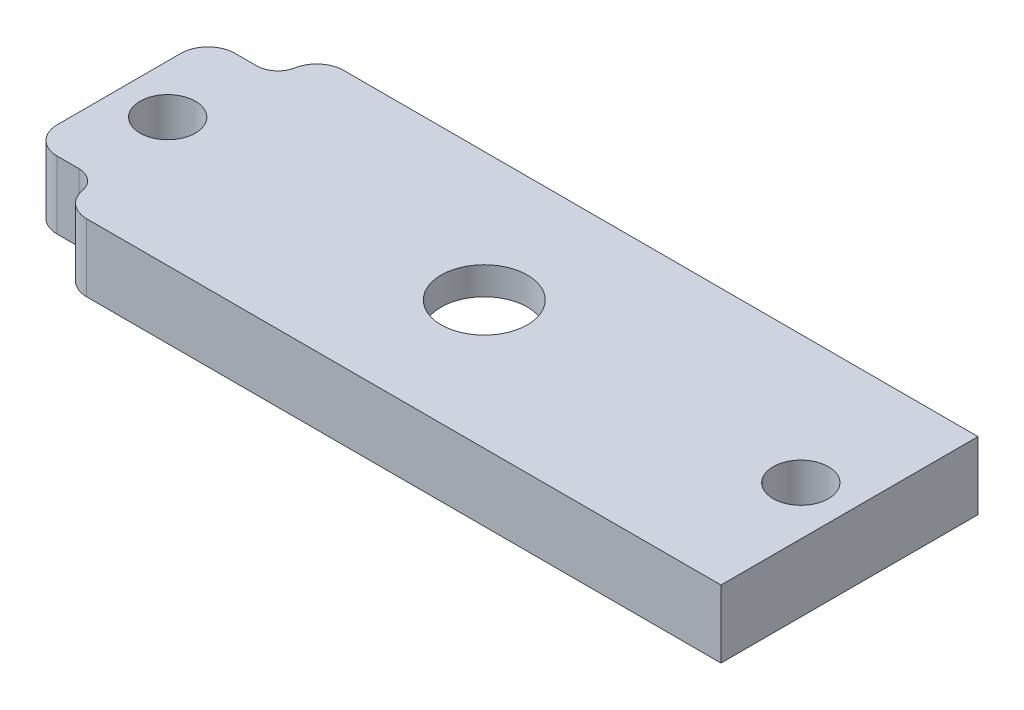
SolidWorks part; units mm, degrees
ref_plane "Front Plane" through (0, 0, 0) normal (0, 0, 1) x (1, 0, 0)
ref_plane "Top Plane" through (0, 0, 0) normal (0, 1, 0) x (1, 0, 0)
ref_plane "Right Plane" through (0, 0, 0) normal (1, 0, 0) x (0, 0, -1)
sketch "Sketch2" plane through (0, 0, 0) normal (0, 1, 0) x (1, 0, 0)
  line L1 (0, 0) -> (68.58, 0)
  line L2 (0, 0) -> (0, 24.13)
  line L3 (0, 24.13) -> (68.58, 24.13)
  line L4 (68.58, 0) -> (68.58, 24.13)
  circle A0 centre (4.57, 12.065) radius 2.6
  circle A1 centre (64.01, 12.065) radius 2.6
  point P10 (68.58, 12.065)
  dimension "D4" = 5.2
  dimension "D1" = 68.58
  dimension "D2" = 24.13
  dimension "D3" = 4.57
  dimension "D5" = 4.57
extrude "Boss-Extrude1" add sketch "Sketch2" along normal blind 6.35
sketch "Sketch3" plane through (0, 6.35, 0) normal (0, 1, 0) x (1, 0, 0)
  line L0 (6.57, 22.415) -> (6.57, 24.13)
  line L2 (4.57, 20.415) -> (0, 20.415)
  line L3 (0, 24.13) -> (0, 0) construction
  line L4 (68.58, 24.13) -> (0, 24.13) construction
  line L5 (4.57, 12.065) -> (64.01, 12.065) construction
  line L6 (34.29, 24.13) -> (34.29, 0) construction
  line L7 (0, 0) -> (68.58, 0) construction
  line L8 (6.57, 1.715) -> (6.57, 0)
  line L9 (4.57, 3.715) -> (0, 3.715)
  arc A0 (4.57, 20.415) -> (6.57, 22.415) centre (4.57, 22.415) ccw
  circle A1 centre (4.57, 12.065) radius 2.6 construction
  circle A2 centre (4.57, 12.065) radius 2.6
  arc A3 (4.57, 3.715) -> (6.57, 1.715) centre (4.57, 1.715) cw
  line M1 (0, 0) -> (68.58, 0)
  line M5 (68.58, 24.13) -> (0, 24.13)
  line M7 (0, 24.13) -> (0, 0)
  dimension "D1" = 10.35
  dimension "D2" = 4
extrude "Cut-Extrude1" cut sketch "Sketch3" against normal through all contours A3 L9 L8 M7 M1 | L2 A0 L0 M5 M7
fillet "Fillet3" radius 2.54 4 edges at (6.57, 3.175, 0) (0, 3.175, -3.715) (0, 3.175, -20.415) (6.57, 3.175, -24.13)
sketch "Sketch4" plane through (0, 6.35, 0) normal (0, 1, 0) x (1, 0, 0)
  line L0 (4.57, 12.065) -> (64.01, 12.065) construction
  circle A0 centre (34.29, 12.065) radius 4.05
  circle A1 centre (4.57, 12.065) radius 2.6 construction
  circle A2 centre (64.01, 12.065) radius 2.6 construction
  circle A3 centre (64.01, 12.065) radius 2.6 construction
  circle A4 centre (4.57, 12.065) radius 2.6 construction
  point P8 (34.29, 12.065)
  dimension "D1" = 8.1
extrude "Cut-Extrude2" cut sketch "Sketch4" against normal through all
ref_plane "Plane2" through (34.29, 0, 0) normal (1, 0, 0) x (0, 0, -1)
sketch "Sketch8" plane through (34.29, 0, 0) normal (1, 0, 0) x (0, 0, -1)
  line L0 (0, 6.35) -> (24.13, 6.35) construction
  line L1 (0, 6.35) -> (24.13, 6.35) construction
  line L2 (12.065, 6.35) -> (12.065, 0) construction
  line L3 (0, 0) -> (24.13, 0) construction
  line L4 (22.13, 0) -> (24.13, 0) construction
  line L5 (12.065, 4.35) -> (12.065, 0)
  line L6 (0, 0) -> (24.13, 0)
  circle A0 centre (12.065, -9.4692) radius 13.8192
  point P8 (12.065, 4.35)
  dimension "D1" = 2
  dimension "D2" = 2
revolve "Cut-Revolve6" cut sketch "Sketch8" angle 360 about L2
